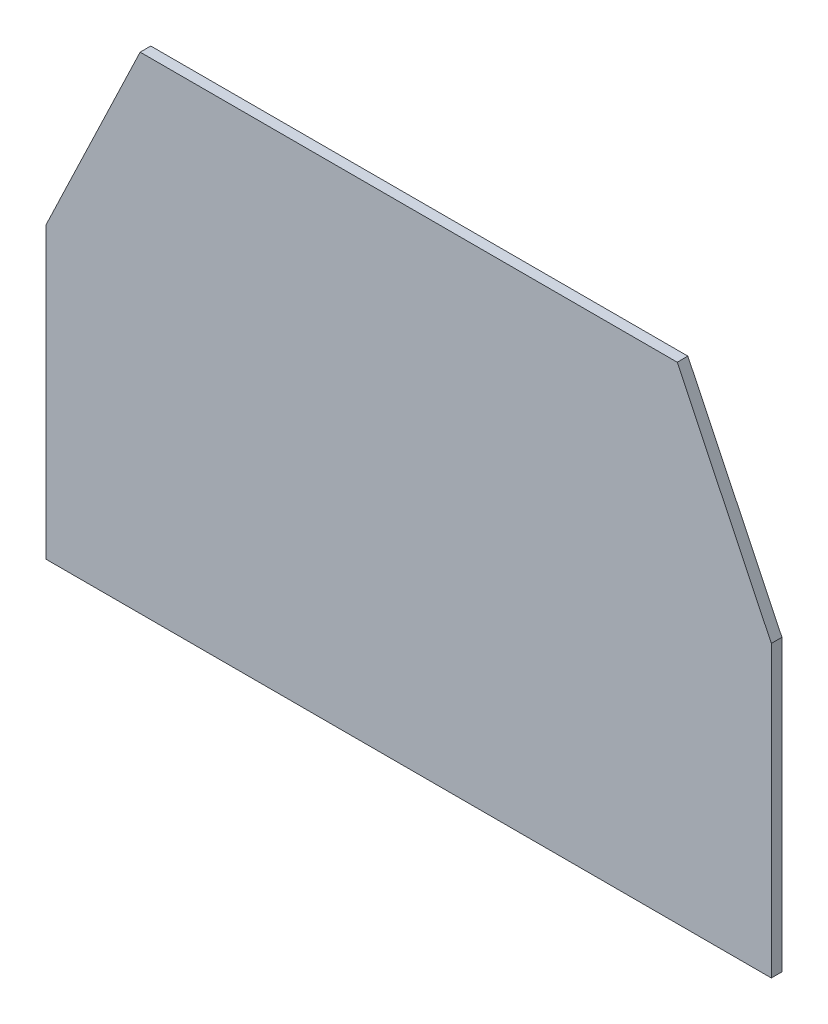
SolidWorks part; units mm, degrees
ref_plane "Ebene vorne" through (0, 0, 0) normal (0, 0, 1) x (1, 0, 0)
ref_plane "Ebene oben" through (0, 0, 0) normal (0, 1, 0) x (1, 0, 0)
ref_plane "Ebene rechts" through (0, 0, 0) normal (1, 0, 0) x (0, 0, -1)
sketch "Skizze1" plane through (0, 0, 0) normal (0, 0, 1) x (1, 0, 0)
  line L2 (341.8583, -194.3676) -> (-341.8583, -194.3676)
  line L11 (-341.8583, -194.3676) -> (-341.8583, 78.7946)
  line L14 (-341.8583, 78.7946) -> (-253.157, 264.0237)
  line L15 (253.157, 264.0237) -> (-253.157, 264.0237)
  line L32 (341.8583, 78.7946) -> (253.157, 264.0237)
  line L39 (341.8583, -194.3676) -> (341.8583, 78.7946)
extrude "Aufsatz-Linear austragen1" add sketch "Skizze1" along normal blind 10
